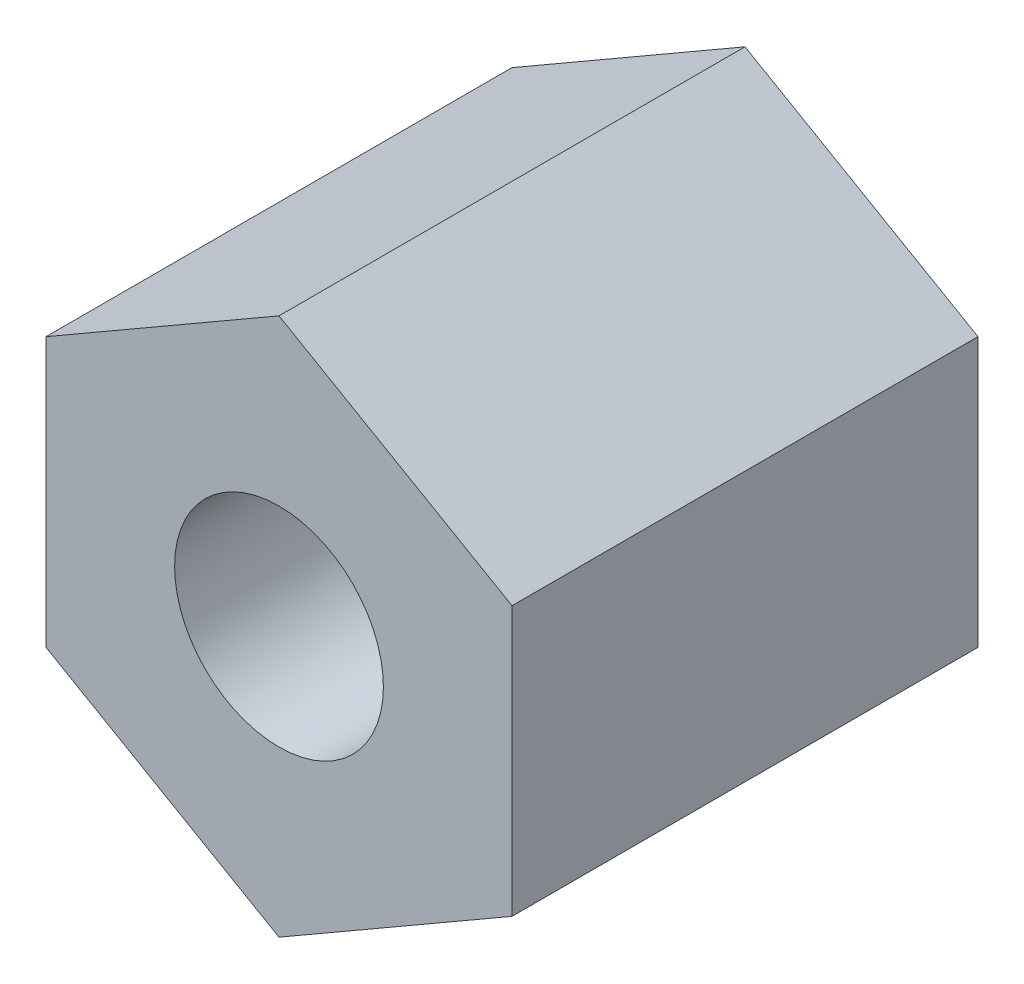
SolidWorks part; units mm, degrees
ref_plane "Front Plane" through (0, 0, 0) normal (0, 0, 1) x (1, 0, 0)
ref_plane "Top Plane" through (0, 0, 0) normal (0, 1, 0) x (1, 0, 0)
ref_plane "Right Plane" through (0, 0, 0) normal (1, 0, 0) x (0, 0, -1)
sketch "Sketch2" plane through (0, 0, 0) normal (0, 0, 1) x (1, 0, 0)
  line L0 (0, 3.6662) -> (3.175, 1.8331)
  line L1 (3.175, 1.8331) -> (3.175, -1.8331)
  line L2 (3.175, -1.8331) -> (0, -3.6662)
  line L3 (0, -3.6662) -> (-3.175, -1.8331)
  line L4 (-3.175, -1.8331) -> (-3.175, 1.8331)
  line L5 (-3.175, 1.8331) -> (0, 3.6662)
  circle A4 centre (0, 0) radius 1.4224
  point P16 (3.175, 0)
  dimension "D4" = 2.8448
  dimension "D1" = 6.35
  dimension "D2" = 6.35
  dimension "D3" = 7.3323
extrude "Boss-Extrude1" add sketch "Sketch2" along normal blind 6.35
